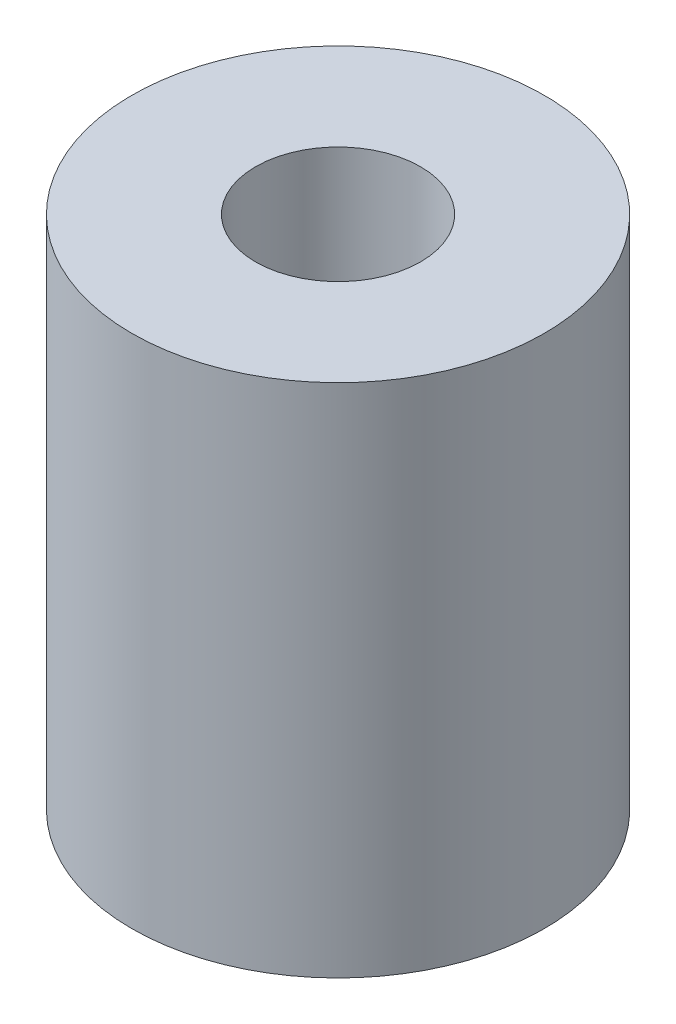
SolidWorks part; units mm, degrees
ref_plane "Front Plane" through (0, 0, 0) normal (0, 0, 1) x (1, 0, 0)
ref_plane "Top Plane" through (0, 0, 0) normal (0, 1, 0) x (1, 0, 0)
ref_plane "Right Plane" through (0, 0, 0) normal (1, 0, 0) x (0, 0, -1)
sketch "Sketch1" plane through (0, 0, 0) normal (0, 1, 0) x (1, 0, 0)
  circle A0 centre (0, 0) radius 1.6
  circle A1 centre (0, 0) radius 4
  dimension "D1" = 3.2
  dimension "D2" = 8
extrude "Boss-Extrude1" add sketch "Sketch1" along normal blind 10
